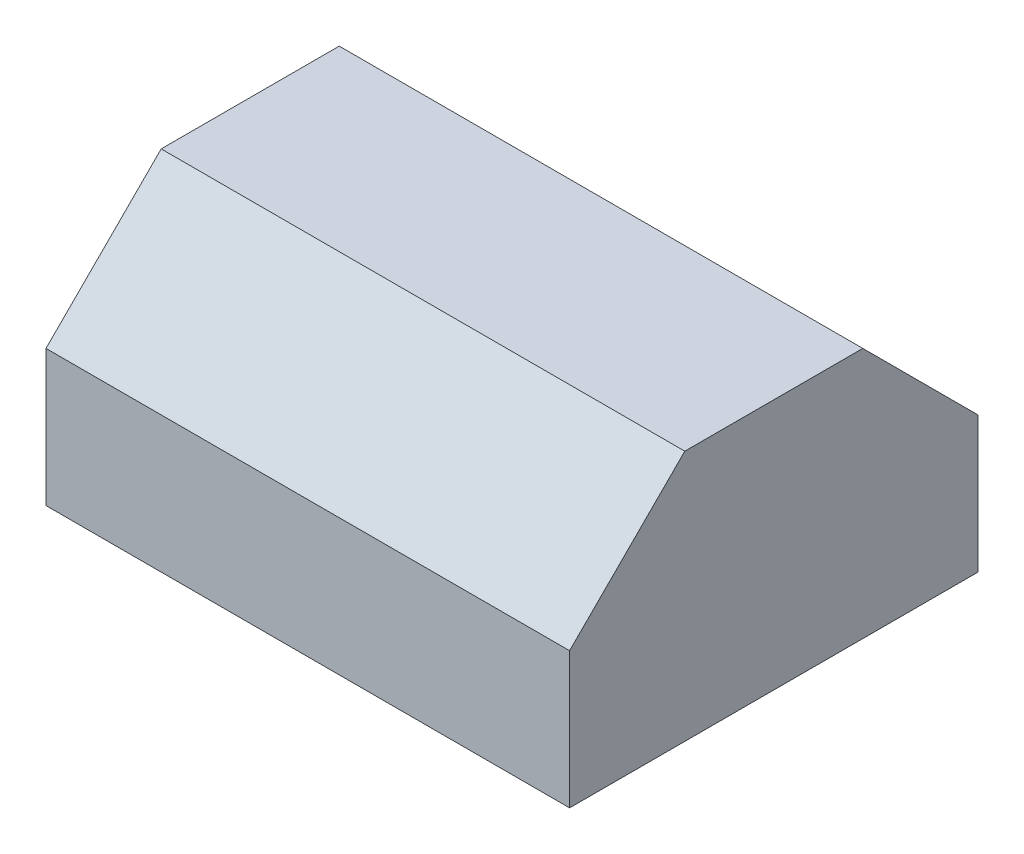
SolidWorks part; units mm, degrees
ref_plane "Front Plane" through (0, 0, 0) normal (0, 0, 1) x (1, 0, 0)
ref_plane "Top Plane" through (0, 0, 0) normal (0, 1, 0) x (1, 0, 0)
ref_plane "Right Plane" through (0, 0, 0) normal (1, 0, 0) x (0, 0, -1)
sketch "Sketch1" plane through (0, 0, 0) normal (1, 0, 0) x (0, 0, -1)
  line L0 (0, 0) -> (195, 0)
  line L1 (195, 0) -> (195, 65)
  line L2 (195, 65) -> (140, 120)
  line L3 (140, 120) -> (55, 120)
  line L4 (55, 120) -> (0, 65)
  line L5 (0, 65) -> (0, 0)
  line L6 (0, 0) -> (0.4355, 0.9265)
  dimension "D1" = 195
  dimension "D2" = 65
  dimension "D3" = 65
  dimension "D4" = 45
  dimension "D5" = 45
  dimension "D6" = 85
extrude "Boss-Extrude1" add sketch "Sketch1" along normal blind 250
shell "Shell1" thickness 5
sketch "Sketch4" plane through (0, 0, 0) normal (0, -1, 0) x (1, 0, 0)
  line L0 (250, -195) -> (0, -195) construction
  line L1 (10, -195) -> (20, -195)
  line L2 (10, -195) -> (10, -190)
  line L3 (10, -190) -> (20, -190)
  line L4 (20, -195) -> (20, -190)
  line L5 (0, 0) -> (0, -195) construction
  line L46 (230, -190) -> (240, -190)
  line L47 (240, -195) -> (240, -190)
  line L48 (230, -195) -> (240, -195)
  line L49 (230, -195) -> (230, -190)
  line L50 (30, -190) -> (40, -190) [skipped]
  line L51 (40, -195) -> (40, -190) [skipped]
  line L52 (30, -195) -> (40, -195) [skipped]
  line L53 (30, -195) -> (30, -190) [skipped]
  line L54 (50, -190) -> (60, -190) [skipped]
  line L55 (60, -195) -> (60, -190) [skipped]
  line L56 (50, -195) -> (60, -195) [skipped]
  line L57 (50, -195) -> (50, -190) [skipped]
  line L58 (70, -190) -> (80, -190) [skipped]
  line L59 (80, -195) -> (80, -190) [skipped]
  line L60 (70, -195) -> (80, -195) [skipped]
  line L61 (70, -195) -> (70, -190) [skipped]
  line L62 (90, -190) -> (100, -190) [skipped]
  line L63 (100, -195) -> (100, -190) [skipped]
  line L64 (90, -195) -> (100, -195) [skipped]
  line L65 (90, -195) -> (90, -190) [skipped]
  line L66 (110, -190) -> (120, -190) [skipped]
  line L67 (120, -195) -> (120, -190) [skipped]
  line L68 (110, -195) -> (120, -195) [skipped]
  line L69 (110, -195) -> (110, -190) [skipped]
  line L70 (130, -190) -> (140, -190) [skipped]
  line L71 (140, -195) -> (140, -190) [skipped]
  line L72 (130, -195) -> (140, -195) [skipped]
  line L73 (130, -195) -> (130, -190) [skipped]
  line L74 (150, -190) -> (160, -190) [skipped]
  line L75 (160, -195) -> (160, -190) [skipped]
  line L76 (150, -195) -> (160, -195) [skipped]
  line L77 (150, -195) -> (150, -190) [skipped]
  line L78 (170, -190) -> (180, -190) [skipped]
  line L79 (180, -195) -> (180, -190) [skipped]
  line L80 (170, -195) -> (180, -195) [skipped]
  line L81 (170, -195) -> (170, -190) [skipped]
  line L82 (190, -190) -> (200, -190) [skipped]
  line L83 (200, -195) -> (200, -190) [skipped]
  line L84 (190, -195) -> (200, -195) [skipped]
  line L85 (190, -195) -> (190, -190) [skipped]
  line L86 (210, -195) -> (220, -195) [skipped]
  line L87 (210, -195) -> (210, -190) [skipped]
  line L88 (220, -195) -> (220, -190) [skipped]
  line L89 (210, -190) -> (220, -190) [skipped]
  dimension "D1" = 5
  dimension "D2" = 10
  dimension "D3" = 10
  dimension "D4" = 12
extrude "Boss-Extrude3" add sketch "Sketch4" along normal blind 5
sketch "Sketch5" plane through (240, 0, 0) normal (1, 0, 0) x (0, 0, -1)
  line L0 (190, -5) -> (190, 0) construction
  line L1 (195, -5) -> (190, -5) construction
  circle A0 centre (192.5, -2.5) radius 1.25
  dimension "D1" = 2.5
  dimension "D2" = 2.5
  dimension "D3" = 2.5
extrude "Cut-Extrude3" cut sketch "Sketch5" against normal through all
fillet "Fillet2" radius 2 4 edges at (235, -5, -195) (235, -5, -190) (15, -5, -190) (15, -5, -195)
